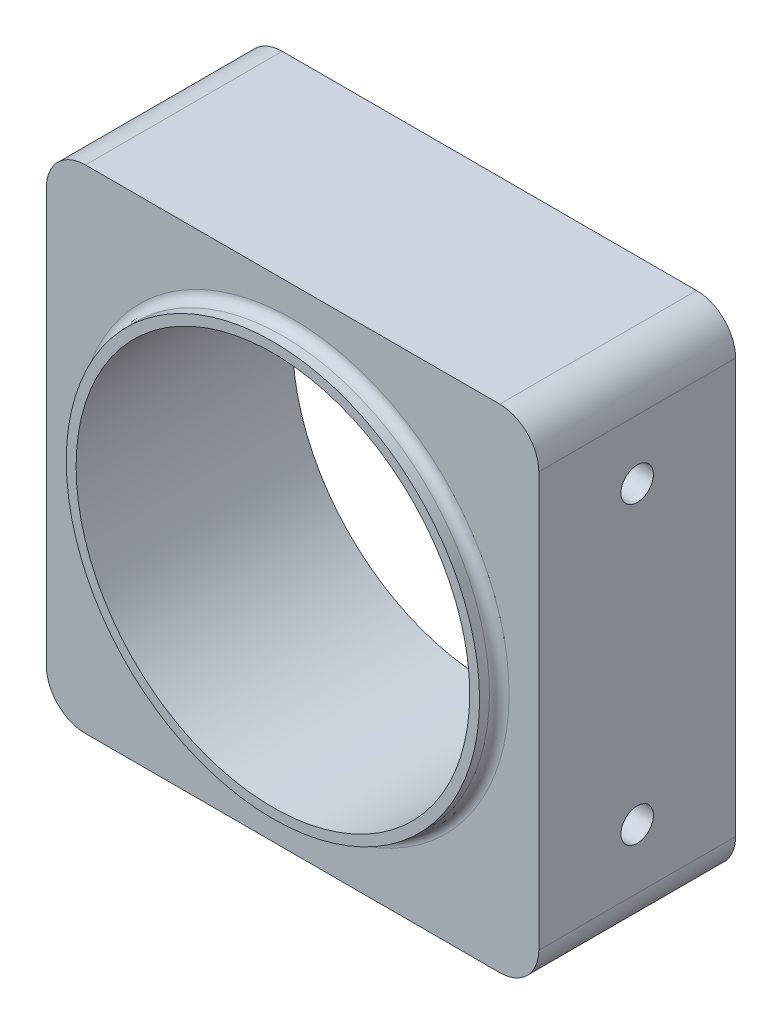
SolidWorks part; units mm, degrees
material "6061 Alloy"
ref_plane "Front Plane" through (0, 0, 0) normal (0, 0, 1) x (1, 0, 0)
ref_plane "Top Plane" through (0, 0, 0) normal (0, 1, 0) x (1, 0, 0)
ref_plane "Right Plane" through (0, 0, 0) normal (1, 0, 0) x (0, 0, -1)
sketch "Sketch1" plane through (0, 0, 0) normal (0, 0, 1) x (1, 0, 0)
  line L1 (-25.019, -25.019) -> (25.019, -25.019)
  line L2 (-25.019, -25.019) -> (-25.019, 25.019)
  line L3 (-25.019, 25.019) -> (25.019, 25.019)
  line L4 (25.019, -25.019) -> (25.019, 25.019)
  line L5 (-25.019, -25.019) -> (25.019, 25.019) construction
  line L6 (-25.019, 25.019) -> (25.019, -25.019) construction
  circle A0 centre (0, 0) radius 20
  dimension "D1" = 40
  dimension "D2" = 50.038
  dimension "D3" = 50.038
extrude "Boss-Extrude1" add sketch "Sketch1" along normal blind 20
fillet "Fillet1" radius 3.9688 4 edges at (25.019, 25.019, 10) (25.019, -25.019, 10) (-25.019, -25.019, 10) (-25.019, 25.019, 10)
hole_wizard "M4x0.7 Tapped Hole2" positions "Sketch4" profile "Sketch5" tap size "M4x0.7" standard "ANSI Metric"
sketch "Sketch4" plane through (-25.019, 0, 0) normal (-1, 0, 0) x (0, 0, 1)
  line L0 (11, 0) -> (-11, 0) construction
  line L1 (0, -27.5209) -> (0, 27.5209) construction
  point P0 (10, 15)
  point P2 (10, -15)
  dimension "D1" = 15
  dimension "D2" = 15
  dimension "D3" = 10
sketch "Sketch5" plane through (-25.019, 15, 10) normal (0, 1, 0) x (0, 0, 1)
  line L0 (0, 0) -> (0, 8)
  line L1 (0, 8) -> (1.65, 7.0086)
  line L2 (1.65, 7.0086) -> (1.65, 0)
  line L5 (1.65, 0) -> (0, 0)
  line L10 (0, 8) -> (-1.65, 7.0086) construction
  line L11 (0, -6.35) -> (0, 107.95) construction
  dimension "Tap Drill Dia." = 3.3
  dimension "Tap Drill Depth" = 8
  dimension "Drill Angle" = 118
cosmetic thread "Hole Thread2" parameters "D1"=8, "D2"=4
cosmetic thread "Hole Thread3" parameters "D1"=8, "D2"=4
mirror "Mirror1" about plane through (0, 0, 0) normal (1, 0, 0) of "M4x0.7 Tapped Hole2"
cosmetic thread "Hole Thread4" parameters "D1"=8, "D2"=4
cosmetic thread "Hole Thread5" parameters "D1"=8, "D2"=4
sketch "Sketch6" plane through (0, 0, 20) normal (0, 0, 1) x (1, 0, 0)
  circle A0 centre (0, 0) radius 20
  circle A1 centre (0, 0) radius 21
  dimension "D1" = 40
  dimension "D2" = 42
extrude "Boss-Extrude2" add sketch "Sketch6" along normal blind 2
fillet "Fillet2" radius 1 1 edges at (-21, 0, 20)
